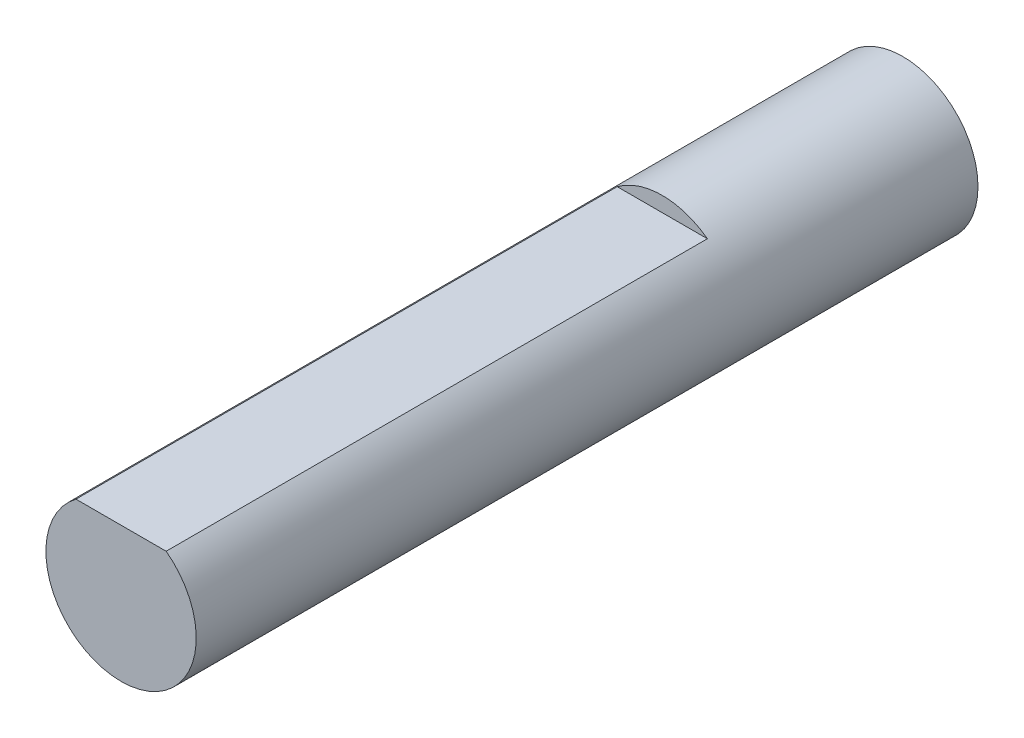
SolidWorks part; units mm, degrees
ref_plane "Alzado" through (0, 0, 0) normal (0, 0, 1) x (1, 0, 0)
ref_plane "Planta" through (0, 0, 0) normal (0, 1, 0) x (1, 0, 0)
ref_plane "Vista lateral" through (0, 0, 0) normal (1, 0, 0) x (0, 0, -1)
sketch "Sketch1" plane through (0, 0, 0) normal (0, 0, 1) x (1, 0, 0)
  circle A0 centre (-10.7405, 9.6856) radius 2.5
extrude "Boss-Extrude1" add sketch "Sketch1" along normal blind 26
sketch "Sketch2" plane through (0, 0, 26) normal (0, 0, 1) x (1, 0, 0)
  line L0 (-10.7405, 11.6856) -> (-10.7405, 7.1856) construction
  line L2 (-12.4339, 11.6856) -> (-9.0103, 11.6856)
  line L3 (-12.4339, 11.6856) -> (-12.4339, 12.1993)
  line L4 (-12.4339, 12.1993) -> (-9.0103, 12.1993)
  line L5 (-9.0103, 11.6856) -> (-9.0103, 12.1993)
  circle A0 centre (-10.7405, 9.6856) radius 2.5 construction
  dimension "D1" = 4.5
extrude "Cut-Extrude2" cut sketch "Sketch2" against normal blind 18
